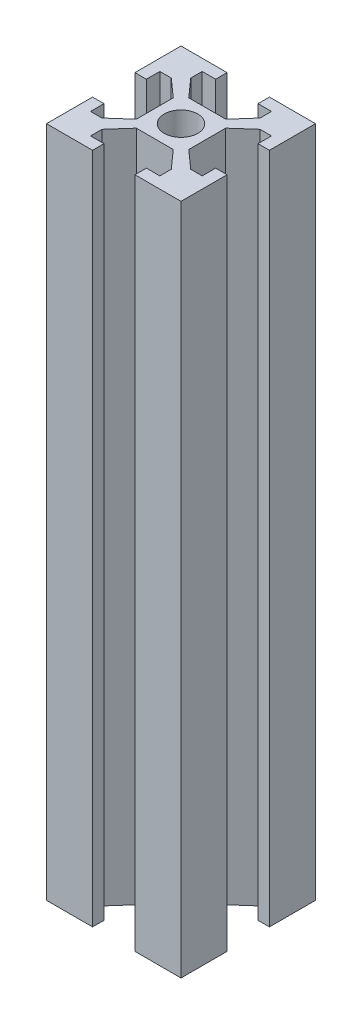
SolidWorks part; units mm, degrees
ref_plane "前视基准面" through (0, 0, 0) normal (0, 0, 1) x (1, 0, 0)
ref_plane "上视基准面" through (0, 0, 0) normal (0, 1, 0) x (1, 0, 0)
ref_plane "右视基准面" through (0, 0, 0) normal (1, 0, 0) x (0, 0, -1)
sketch "草图1" plane through (0, 0, 0) normal (0, 1, 0) x (1, 0, 0)
  line L1 (-10, 10) -> (10, 10)
  line L2 (-10, 10) -> (-10, -10)
  line L3 (-10, -10) -> (10, -10)
  line L4 (10, 10) -> (10, -10)
  line L5 (-10, 10) -> (10, -10) construction
  line L6 (-10, -10) -> (10, 10) construction
  point P0 (0, 0)
  dimension "D1" = 20
  dimension "D2" = 20
extrude "凸台-拉伸1" add sketch "草图1" along normal blind 100
sketch "草图2" plane through (0, 100, 0) normal (0, 1, 0) x (1, 0, 0)
  line L0 (0, 0) -> (0, 13.0428) construction
  line L1 (0, 0) -> (15.5008, 0) construction
  line L2 (-3.15, 10) -> (-3.15, 8.3)
  line L3 (10, 10) -> (-10, 10) construction
  line L4 (-3.15, 8.3) -> (-5.15, 8.3)
  line L5 (-5.15, 8.3) -> (-5.15, 6.6)
  line L6 (-5.15, 6.6) -> (-2.75, 3.9)
  line L7 (-2.75, 3.9) -> (2.75, 3.9)
  line L8 (-3.15, 10) -> (3.15, 10)
  line L9 (5.15, 6.6) -> (2.75, 3.9)
  line L10 (5.15, 8.3) -> (5.15, 6.6)
  line L11 (3.15, 8.3) -> (5.15, 8.3)
  line L12 (3.15, 10) -> (3.15, 8.3)
  line L13 (3.9, 2.75) -> (3.9, -2.75)
  line L14 (6.6, -5.15) -> (3.9, -2.75)
  line L15 (8.3, -5.15) -> (6.6, -5.15)
  line L16 (8.3, -3.15) -> (8.3, -5.15)
  line L17 (10, -3.15) -> (8.3, -3.15)
  line L18 (10, 3.15) -> (10, -3.15)
  line L19 (10, 3.15) -> (8.3, 3.15)
  line L20 (8.3, 3.15) -> (8.3, 5.15)
  line L21 (8.3, 5.15) -> (6.6, 5.15)
  line L22 (6.6, 5.15) -> (3.9, 2.75)
  line L23 (2.75, -3.9) -> (-2.75, -3.9)
  line L24 (-5.15, -6.6) -> (-2.75, -3.9)
  line L25 (-5.15, -8.3) -> (-5.15, -6.6)
  line L26 (-3.15, -8.3) -> (-5.15, -8.3)
  line L27 (-3.15, -10) -> (-3.15, -8.3)
  line L28 (3.15, -10) -> (-3.15, -10)
  line L29 (3.15, -10) -> (3.15, -8.3)
  line L30 (3.15, -8.3) -> (5.15, -8.3)
  line L31 (5.15, -8.3) -> (5.15, -6.6)
  line L32 (5.15, -6.6) -> (2.75, -3.9)
  line L33 (-3.9, -2.75) -> (-3.9, 2.75)
  line L34 (-6.6, 5.15) -> (-3.9, 2.75)
  line L35 (-8.3, 5.15) -> (-6.6, 5.15)
  line L36 (-8.3, 3.15) -> (-8.3, 5.15)
  line L37 (-10, 3.15) -> (-8.3, 3.15)
  line L38 (-10, -3.15) -> (-10, 3.15)
  line L39 (-10, -3.15) -> (-8.3, -3.15)
  line L40 (-8.3, -3.15) -> (-8.3, -5.15)
  line L41 (-8.3, -5.15) -> (-6.6, -5.15)
  line L42 (-6.6, -5.15) -> (-3.9, -2.75)
  circle A0 centre (0, 0) radius 2.5
  point P15 (0, 3.9)
  point P19 (0, 10)
  point P52 (0, 0)
  dimension "D1" = 5
  dimension "D2" = 3.15
  dimension "D3" = 1.7
  dimension "D4" = 2
  dimension "D5" = 1.7
  dimension "D6" = 2.75
  dimension "D7" = 6.1
  dimension "D8" = 4
extrude "切除-拉伸1" cut sketch "草图2" against normal through all
